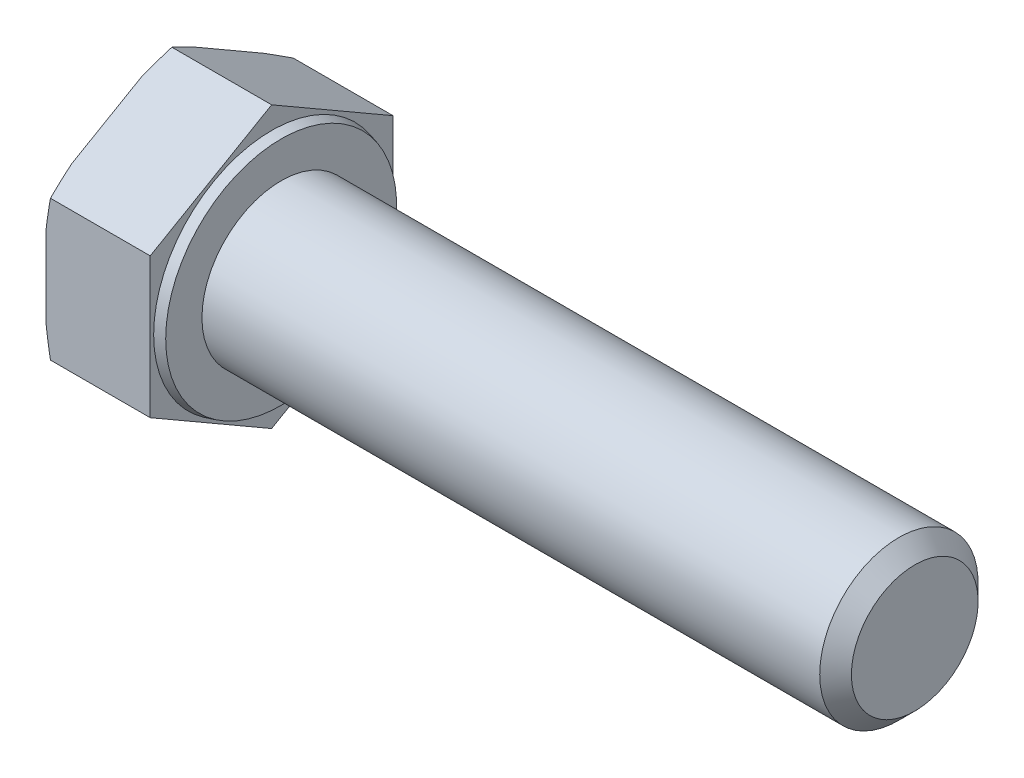
SolidWorks part; units mm, degrees
material "AISI 1020"
ref_plane "Спереди" through (0, 0, 0) normal (0, 0, 1) x (1, 0, 0)
ref_plane "Сверху" through (0, 0, 0) normal (0, 1, 0) x (1, 0, 0)
ref_plane "Справа" through (0, 0, 0) normal (1, 0, 0) x (0, 0, -1)
sketch "Эскиз1" plane through (0, 0, 0) normal (0, 0, 1) x (1, 0, 0)
  line L0 (-1000, 0) -> (49000, 0) construction
  line L1 (-6.58, 0) -> (-6.58, 8.85)
  line L2 (-6.58, 8.85) -> (0, 8.85)
  line L3 (0, 8.85) -> (0, 7.449)
  line L4 (0.6, 5) -> (40.6, 5)
  line L5 (40.6, 5) -> (40.6, 0)
  line L6 (-6.58, 0) -> (40.6, 0)
  line L7 (0, 7.449) -> (0.6, 7.2882)
  line L8 (0.6, 7.2882) -> (0.6, 5)
  line L9 (0.5, 0) -> (0.5, 7.315) construction
  dimension "_d" = 10
  dimension "D1" = 40
  dimension "D5" = 17.7
  dimension "D2" = 0.6
  dimension "D3" = 6.58
  dimension "D4" = 0.1
  dimension "D6" = 14.63
  dimension "D7" = 75
revolve "Повернуть1" add sketch "Эскиз1" angle 360 about L0
cosmetic thread "Условное изображение резьбы1" parameters "D1"=26, "D2"=8.344
sketch "Эскиз2" plane through (-6.58, 0, 0) normal (-1, 0, 0) x (0, 0, 1)
  line L1 (0, -8.85) -> (7.6643, -4.425)
  line L2 (7.6643, -4.425) -> (7.6643, 4.425)
  line L3 (7.6643, 4.425) -> (0, 8.85)
  line L4 (0, 8.85) -> (-7.6643, 4.425)
  line L5 (-7.6643, 4.425) -> (-7.6643, -4.425)
  line L6 (-7.6643, -4.425) -> (0, -8.85)
  circle A0 centre (0, 0) radius 7.6643 construction
  circle A1 centre (0, 0) radius 8.85 construction
extrude "Вырез-Вытянуть1" cut sketch "Эскиз2" against normal through all flip side to cut
sketch "Эскиз4" plane through (0, 0, 0) normal (0, 0, 1) x (1, 0, 0)
  line L0 (-1000, 0) -> (49000, 0) construction
  line L1 (-6.58, 8.075) -> (-6.2979, 8.85)
  line L2 (-6.2979, 8.85) -> (-6.58, 8.85)
  line L3 (-6.58, 8.85) -> (-6.58, 8.075)
  line L4 (-6.58, 4.425) -> (-6.58, 8.85) construction
  line L6 (0, 8.85) -> (-6.58, 8.85) construction
  dimension "D1" = 20
  dimension "D2" = 16.15
revolve "Вырез-Повернуть1" cut sketch "Эскиз4" angle 360 about L0
chamfer "Фаска1" distance 1 angle 45 1 edges at (40.6, 0, 5)
equation "\"l\"= 40'длина болта"
equation "\"_d\"= 10'диаметр болта"
equation "\"b\"= 20'длина резьбы"
equation "\"k\"= 6.58'толщина шляпки"
equation "\"e\"= 17.7'диаметр головки описанный"
equation "\"S\"= 17'размер под ключ"
equation "\"_d@Эскиз1\"=\"_d\""
equation "\"dw\"= 14.63"
equation "\"da\"= 9.78"
equation "\"с\"= 0.6"
equation "\"D1@Эскиз1\"=\"l\""
equation "\"D5@Эскиз1\"=\"e\""
equation "\"D2@Эскиз1\"=\"с\""
equation "\"D3@Эскиз1\"=\"k\""
equation "\"D2@Эскиз4\"=\"S\"*0.95"
equation "\"D1@Фаска1\"=\"_d\"/10"
equation "\"D6@Эскиз1\"=\"dw\""
